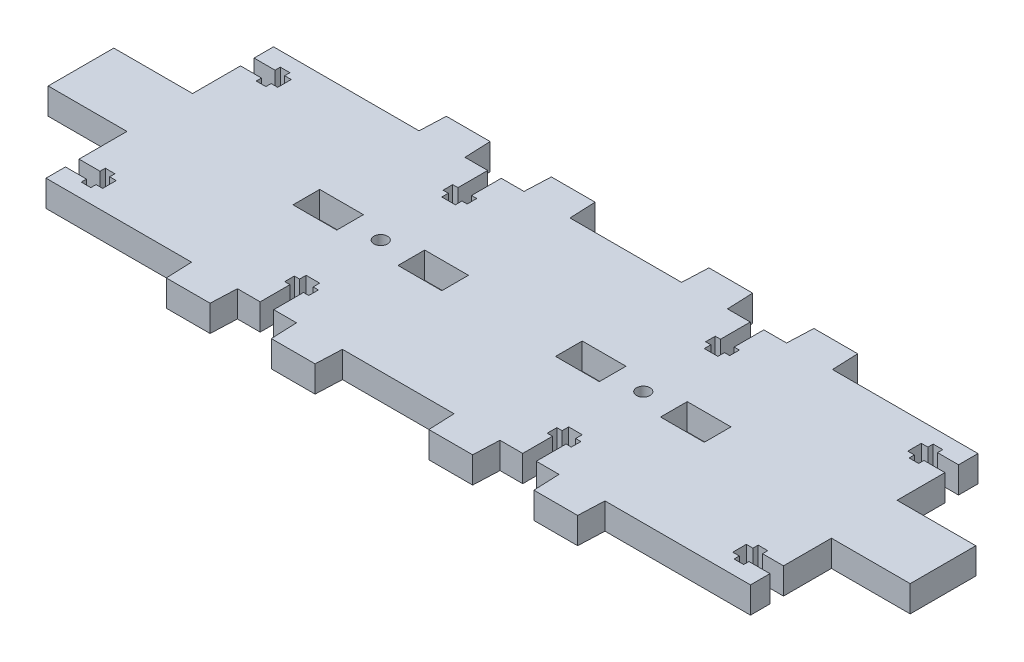
SolidWorks part; units mm, degrees
ref_plane "Спереди" through (0, 0, 0) normal (0, 0, 1) x (1, 0, 0)
ref_plane "Сверху" through (0, 0, 0) normal (0, 1, 0) x (1, 0, 0)
ref_plane "Справа" through (0, 0, 0) normal (1, 0, 0) x (0, 0, -1)
sketch "Эскиз1" plane through (0, 0, 0) normal (0, 1, 0) x (1, 0, 0)
  line L0 (-25.856, -3.1798) -> (-25.856, 2.9202)
  line L1 (-15.856, -3.1798) -> (-25.856, -3.1798)
  line L2 (-15.856, 2.9202) -> (-15.856, -3.1798)
  line L3 (-25.856, 2.9202) -> (-15.856, 2.9202)
  line L4 (-49.856, -3.1798) -> (-49.856, 2.9202)
  line L5 (-39.856, -3.1798) -> (-49.856, -3.1798)
  line L6 (-39.856, 2.9202) -> (-39.856, -3.1798)
  line L7 (-49.856, 2.9202) -> (-39.856, 2.9202)
  line L8 (10.144, 2.9202) -> (10.144, -3.1798)
  line L9 (10.144, -3.1798) -> (20.144, -3.1798)
  line L10 (20.144, -3.1798) -> (20.144, 2.9202)
  line L11 (20.144, 2.9202) -> (10.144, 2.9202)
  line L12 (10.144, 31.8702) -> (9.894, 25.8702)
  line L13 (20.144, 31.8702) -> (10.144, 31.8702)
  line L14 (20.394, 25.8702) -> (20.144, 31.8702)
  line L15 (25.594, 25.8702) -> (20.394, 25.8702)
  line L16 (25.594, 19.0702) -> (25.594, 25.8702)
  line L17 (24.394, 19.0702) -> (25.594, 19.0702)
  line L18 (24.394, 16.8702) -> (24.394, 19.0702)
  line L19 (25.594, 16.8702) -> (24.394, 16.8702)
  line L20 (25.594, 15.3702) -> (25.594, 16.8702)
  line L21 (28.694, 15.3702) -> (25.594, 15.3702)
  line L22 (28.694, 16.8702) -> (28.694, 15.3702)
  line L23 (29.894, 16.8702) -> (28.694, 16.8702)
  line L24 (29.894, 19.0702) -> (29.894, 16.8702)
  line L25 (28.694, 19.0702) -> (29.894, 19.0702)
  line L26 (28.694, 25.8702) -> (28.694, 19.0702)
  line L27 (33.894, 25.8702) -> (28.694, 25.8702)
  line L28 (34.144, 31.8702) -> (33.894, 25.8702)
  line L29 (44.144, 31.8702) -> (34.144, 31.8702)
  line L30 (44.394, 25.8702) -> (44.144, 31.8702)
  line L31 (77.644, 25.8702) -> (44.394, 25.8702)
  line L32 (77.644, 21.4202) -> (77.644, 25.8702)
  line L33 (72.844, 21.4202) -> (77.644, 21.4202)
  line L34 (72.844, 22.6202) -> (72.844, 21.4202)
  line L35 (70.644, 22.6202) -> (72.844, 22.6202)
  line L36 (70.644, 21.4202) -> (70.644, 22.6202)
  line L37 (69.144, 21.4202) -> (70.644, 21.4202)
  line L38 (69.144, 18.3202) -> (69.144, 21.4202)
  line L39 (70.644, 18.3202) -> (69.144, 18.3202)
  line L40 (70.644, 17.1202) -> (70.644, 18.3202)
  line L41 (72.844, 17.1202) -> (70.644, 17.1202)
  line L42 (72.844, 18.3202) -> (72.844, 17.1202)
  line L43 (77.644, 18.3202) -> (72.844, 18.3202)
  line L44 (77.644, 7.3702) -> (77.644, 18.3202)
  line L45 (95.644, 7.3702) -> (77.644, 7.3702)
  line L46 (95.644, -7.6298) -> (95.644, 7.3702)
  line L47 (77.644, -7.6298) -> (95.644, -7.6298)
  line L48 (77.644, -18.5798) -> (77.644, -7.6298)
  line L49 (72.844, -18.5798) -> (77.644, -18.5798)
  line L50 (72.844, -17.3798) -> (72.844, -18.5798)
  line L51 (70.644, -17.3798) -> (72.844, -17.3798)
  line L52 (70.644, -18.5798) -> (70.644, -17.3798)
  line L53 (69.144, -18.5798) -> (70.644, -18.5798)
  line L54 (69.144, -21.6798) -> (69.144, -18.5798)
  line L55 (70.644, -21.6798) -> (69.144, -21.6798)
  line L56 (70.644, -22.8798) -> (70.644, -21.6798)
  line L57 (72.844, -22.8798) -> (70.644, -22.8798)
  line L58 (72.844, -21.6798) -> (72.844, -22.8798)
  line L59 (77.644, -21.6798) -> (72.844, -21.6798)
  line L60 (77.644, -26.1298) -> (77.644, -21.6798)
  line L61 (44.394, -26.1298) -> (77.644, -26.1298)
  line L62 (44.144, -32.1298) -> (44.394, -26.1298)
  line L63 (34.144, -32.1298) -> (44.144, -32.1298)
  line L64 (33.894, -26.1298) -> (34.144, -32.1298)
  line L65 (28.694, -26.1298) -> (33.894, -26.1298)
  line L66 (28.694, -19.3298) -> (28.694, -26.1298)
  line L67 (29.894, -19.3298) -> (28.694, -19.3298)
  line L68 (29.894, -17.1298) -> (29.894, -19.3298)
  line L69 (28.694, -17.1298) -> (29.894, -17.1298)
  line L70 (28.694, -15.6298) -> (28.694, -17.1298)
  line L71 (25.594, -15.6298) -> (28.694, -15.6298)
  line L72 (25.594, -17.1298) -> (25.594, -15.6298)
  line L73 (24.394, -17.1298) -> (25.594, -17.1298)
  line L74 (24.394, -19.3298) -> (24.394, -17.1298)
  line L75 (25.594, -19.3298) -> (24.394, -19.3298)
  line L76 (25.594, -26.1298) -> (25.594, -19.3298)
  line L77 (20.394, -26.1298) -> (25.594, -26.1298)
  line L78 (20.144, -32.1298) -> (20.394, -26.1298)
  line L79 (10.144, -32.1298) -> (20.144, -32.1298)
  line L80 (9.894, -26.1298) -> (10.144, -32.1298)
  line L81 (-15.606, -26.1298) -> (9.894, -26.1298)
  line L82 (-15.606, -26.1298) -> (-15.856, -32.1298)
  line L83 (-15.856, -32.1298) -> (-25.856, -32.1298)
  line L84 (-25.856, -32.1298) -> (-26.106, -26.1298)
  line L85 (-26.106, -26.1298) -> (-31.306, -26.1298)
  line L86 (-31.306, -26.1298) -> (-31.306, -19.3298)
  line L87 (-31.306, -19.3298) -> (-30.106, -19.3298)
  line L88 (-30.106, -19.3298) -> (-30.106, -17.1298)
  line L89 (-30.106, -17.1298) -> (-31.306, -17.1298)
  line L90 (-31.306, -17.1298) -> (-31.306, -15.6298)
  line L91 (-31.306, -15.6298) -> (-34.406, -15.6298)
  line L92 (-34.406, -15.6298) -> (-34.406, -17.1298)
  line L93 (-34.406, -17.1298) -> (-35.606, -17.1298)
  line L94 (-35.606, -17.1298) -> (-35.606, -19.3298)
  line L95 (-35.606, -19.3298) -> (-34.406, -19.3298)
  line L96 (-34.406, -19.3298) -> (-34.406, -26.1298)
  line L97 (-34.406, -26.1298) -> (-39.606, -26.1298)
  line L98 (-39.606, -26.1298) -> (-39.856, -32.1298)
  line L99 (-39.856, -32.1298) -> (-49.856, -32.1298)
  line L100 (-49.856, -32.1298) -> (-50.106, -26.1298)
  line L101 (-50.106, -26.1298) -> (-83.356, -26.1298)
  line L102 (-83.356, -26.1298) -> (-83.356, -21.6798)
  line L103 (-83.356, -21.6798) -> (-78.556, -21.6798)
  line L104 (-78.556, -21.6798) -> (-78.556, -22.8798)
  line L105 (-78.556, -22.8798) -> (-76.356, -22.8798)
  line L106 (-76.356, -22.8798) -> (-76.356, -21.6798)
  line L107 (-76.356, -21.6798) -> (-74.856, -21.6798)
  line L108 (-74.856, -21.6798) -> (-74.856, -18.5798)
  line L109 (-74.856, -18.5798) -> (-76.356, -18.5798)
  line L110 (-76.356, -18.5798) -> (-76.356, -17.3798)
  line L111 (-76.356, -17.3798) -> (-78.556, -17.3798)
  line L112 (-78.556, -17.3798) -> (-78.556, -18.5798)
  line L113 (-78.556, -18.5798) -> (-83.356, -18.5798)
  line L114 (-83.356, -18.5798) -> (-83.356, -7.6298)
  line L115 (-83.356, -7.6298) -> (-101.356, -7.6298)
  line L116 (-101.356, -7.6298) -> (-101.356, 7.3702)
  line L117 (-101.356, 7.3702) -> (-83.356, 7.3702)
  line L118 (-83.356, 7.3702) -> (-83.356, 18.3202)
  line L119 (-83.356, 18.3202) -> (-78.556, 18.3202)
  line L120 (-78.556, 18.3202) -> (-78.556, 17.1202)
  line L121 (-78.556, 17.1202) -> (-76.356, 17.1202)
  line L122 (-76.356, 17.1202) -> (-76.356, 18.3202)
  line L123 (-76.356, 18.3202) -> (-74.856, 18.3202)
  line L124 (-74.856, 18.3202) -> (-74.856, 21.4202)
  line L125 (-74.856, 21.4202) -> (-76.356, 21.4202)
  line L126 (-76.356, 21.4202) -> (-76.356, 22.6202)
  line L127 (-76.356, 22.6202) -> (-78.556, 22.6202)
  line L128 (-78.556, 22.6202) -> (-78.556, 21.4202)
  line L129 (-78.556, 21.4202) -> (-83.356, 21.4202)
  line L130 (-83.356, 21.4202) -> (-83.356, 25.8702)
  line L131 (-83.356, 25.8702) -> (-50.106, 25.8702)
  line L132 (-50.106, 25.8702) -> (-49.856, 31.8702)
  line L133 (-49.856, 31.8702) -> (-39.856, 31.8702)
  line L134 (-39.856, 31.8702) -> (-39.606, 25.8702)
  line L135 (-39.606, 25.8702) -> (-34.406, 25.8702)
  line L136 (-34.406, 25.8702) -> (-34.406, 19.0702)
  line L137 (-34.406, 19.0702) -> (-35.606, 19.0702)
  line L138 (-35.606, 19.0702) -> (-35.606, 16.8702)
  line L139 (-35.606, 16.8702) -> (-34.406, 16.8702)
  line L140 (-34.406, 16.8702) -> (-34.406, 15.3702)
  line L141 (-34.406, 15.3702) -> (-31.306, 15.3702)
  line L142 (-31.306, 15.3702) -> (-31.306, 16.8702)
  line L143 (-31.306, 16.8702) -> (-30.106, 16.8702)
  line L144 (-30.106, 16.8702) -> (-30.106, 19.0702)
  line L145 (-30.106, 19.0702) -> (-31.306, 19.0702)
  line L146 (-31.306, 19.0702) -> (-31.306, 25.8702)
  line L147 (-31.306, 25.8702) -> (-26.106, 25.8702)
  line L148 (-26.106, 25.8702) -> (-25.856, 31.8702)
  line L149 (-25.856, 31.8702) -> (-15.856, 31.8702)
  line L150 (-15.856, 31.8702) -> (-15.606, 25.8702)
  line L151 (9.894, 25.8702) -> (-15.606, 25.8702)
  line L152 (34.144, 2.9202) -> (34.144, -3.1798)
  line L153 (34.144, -3.1798) -> (44.144, -3.1798)
  line L154 (44.144, -3.1798) -> (44.144, 2.9202)
  line L155 (44.144, 2.9202) -> (34.144, 2.9202)
  circle A0 centre (-32.856, -0.1298) radius 1.55
  circle A1 centre (27.144, -0.1298) radius 1.55
extrude "Бобышка-Вытянуть1" add sketch "Эскиз1" along normal blind 6
